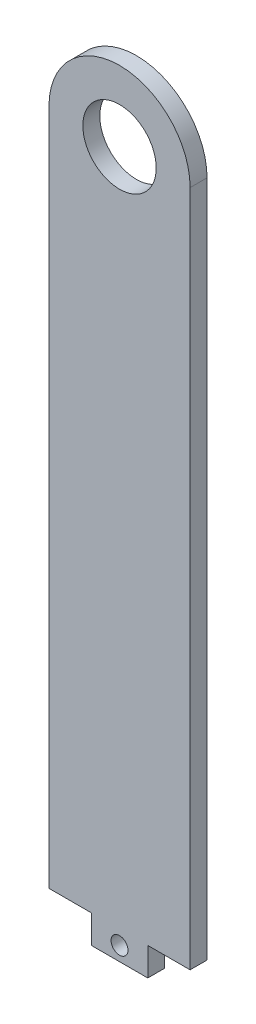
SolidWorks part; units mm, degrees
material "AISI 1030 HR"
ref_plane "Front Plane" through (0, 0, 0) normal (0, 0, 1) x (1, 0, 0)
ref_plane "Top Plane" through (0, 0, 0) normal (0, 1, 0) x (1, 0, 0)
ref_plane "Right Plane" through (0, 0, 0) normal (1, 0, 0) x (0, 0, -1)
sketch "Sketch1" plane through (0, 0, 0) normal (0, 0, 1) x (1, 0, 0)
  line L1 (-25, -120) -> (25, -120)
  line L2 (-25, -120) -> (-25, 120)
  line L4 (25, -120) -> (25, 120)
  line L5 (-25, -120) -> (25, 120) construction
  line L6 (-25, 120) -> (25, -120) construction
  arc A0 (25, 120) -> (-25, 120) centre (0, 120) ccw
  circle A2 centre (0, 120) radius 13
  point P0 (0, 0)
  dimension "D3" = 26
  dimension "D1" = 240
  dimension "D2" = 50
extrude "Boss-Extrude1" add sketch "Sketch1" along normal blind 6
sketch "Sketch2" plane through (0, 0, 0) normal (0, 0, -1) x (-1, 0, 0)
  line L0 (0, -120) -> (0, -130) construction
  line L1 (25, -120) -> (-25, -120) construction
  line L3 (-10, -130) -> (10, -130)
  line L4 (-10, -130) -> (-10, -120)
  line L5 (-10, -120) -> (10, -120)
  line L6 (10, -130) -> (10, -120)
  line L7 (-10, -130) -> (10, -120) construction
  line L8 (-10, -120) -> (10, -130) construction
  circle A0 centre (0, -125) radius 3
  point P5 (0, -125)
  dimension "D3" = 6
  dimension "D1" = 10
  dimension "D2" = 20
extrude "Boss-Extrude2" add sketch "Sketch2" against normal blind 6
